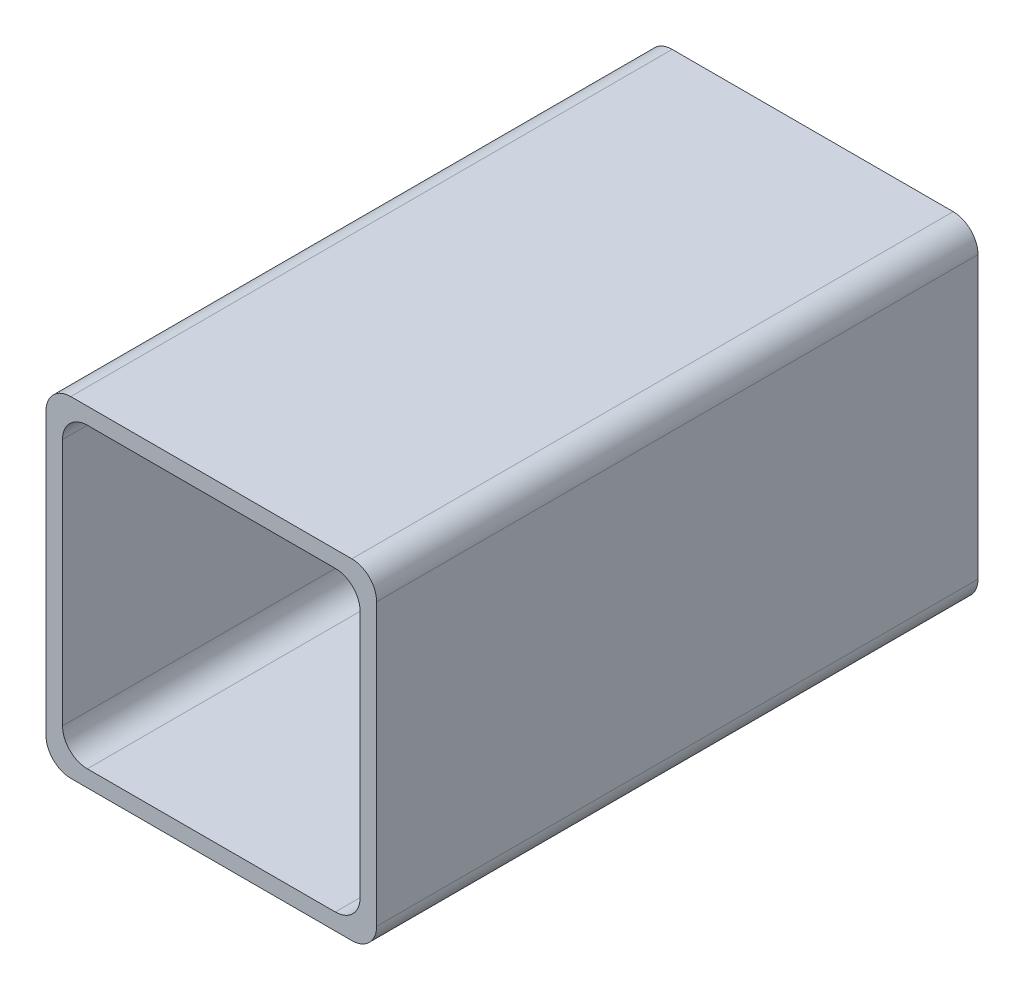
SolidWorks part; units mm, degrees
material "AISI 1020"
ref_plane "Спереди" through (0, 0, 0) normal (0, 0, 1) x (1, 0, 0)
ref_plane "Сверху" through (0, 0, 0) normal (0, 1, 0) x (1, 0, 0)
ref_plane "Справа" through (0, 0, 0) normal (1, 0, 0) x (0, 0, -1)
sketch "Эскиз1" plane through (0, 0, 0) normal (0, 0, 1) x (1, 0, 0)
  line L0 (-199.8423, 0) -> (9792.2745, 0) construction
  line L9 (0, -199.8423) -> (0, 9792.2745) construction
  line L10 (-18, -15) -> (-18, 15)
  line L11 (-15, 18) -> (15, 18)
  line L12 (17, 20) -> (-17, 20)
  line L13 (-20, 17) -> (-20, -17)
  line L14 (17, -20) -> (-17, -20)
  line L15 (-15, -18) -> (15, -18)
  line L16 (20, 17) -> (20, -17)
  line L17 (18, -15) -> (18, 15)
  arc A0 (-17, 20) -> (-20, 17) centre (-17, 17) ccw
  arc A1 (-18, 15) -> (-15, 18) centre (-15, 15) cw
  arc A2 (-18, -15) -> (-15, -18) centre (-15, -15) ccw
  arc A3 (-17, -20) -> (-20, -17) centre (-17, -17) cw
  arc A4 (17, -20) -> (20, -17) centre (17, -17) ccw
  arc A5 (18, -15) -> (15, -18) centre (15, -15) cw
  arc A6 (18, 15) -> (15, 18) centre (15, 15) ccw
  arc A7 (17, 20) -> (20, 17) centre (17, 17) cw
  point P20 (-18, 0)
  point P21 (-20, 0)
  point P24 (0, -20)
  point P25 (0, -18)
  point P26 (0, 18)
  point P27 (0, 20)
  point P35 (20, 0)
  point P36 (18, 0)
  dimension "_Rc" = 3
  dimension "D1" = 3
  dimension "_S" = 2
  dimension "_A" = 40
extrude "Бобышка-Вытянуть1" add sketch "Эскиз1" along normal up to surface (72.75 mm away)
equation "\"D1@Эскиз1\"=\"_Rc@Эскиз1\""
